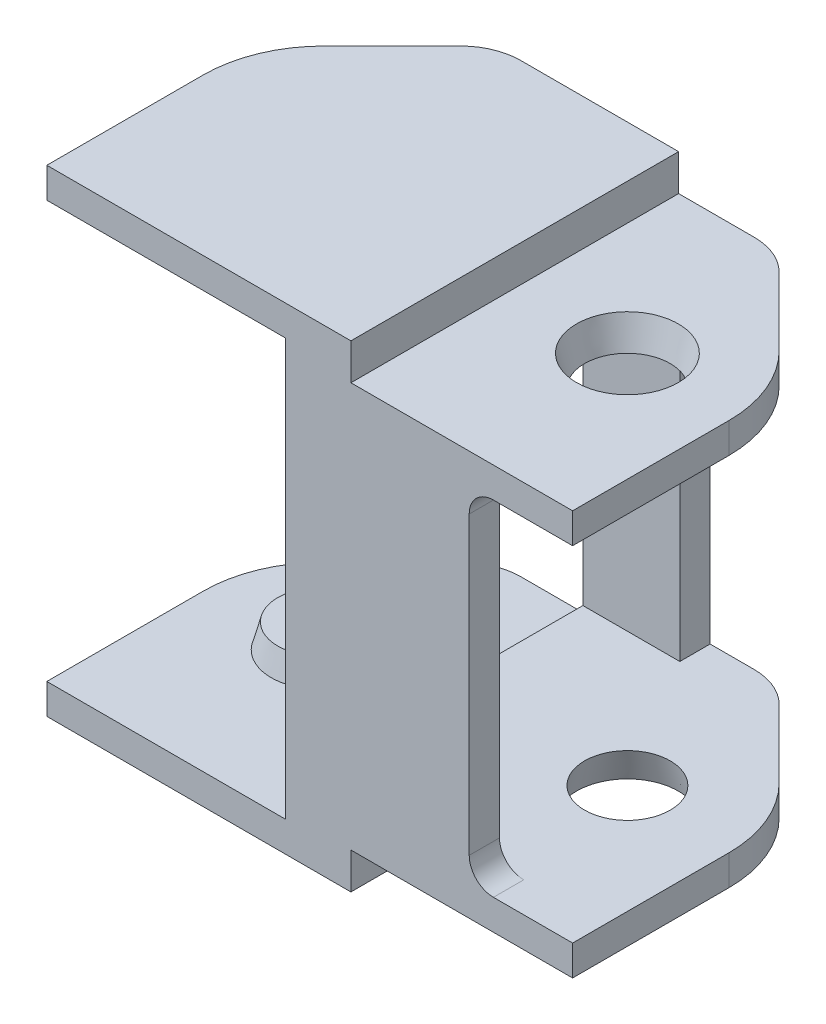
SolidWorks part; units mm, degrees
ref_plane "Front Plane" through (0, 0, 0) normal (0, 0, 1) x (1, 0, 0)
ref_plane "Top Plane" through (0, 0, 0) normal (0, 1, 0) x (1, 0, 0)
ref_plane "Right Plane" through (0, 0, 0) normal (1, 0, 0) x (0, 0, -1)
sketch "Sketch1" plane through (0, 0, 0) normal (0, 0, 1) x (1, 0, 0)
  line L0 (5.35, 1.25) -> (-4.5, 1.25)
  line L1 (9.35, 16.95) -> (9.35, 2.75)
  line L2 (-4.5, 19.7) -> (8.05, 19.7)
  line L3 (5.35, 18.45) -> (5.35, 3.25)
  line L4 (9.35, 2.75) -> (9.3789, 2.6999)
  line L5 (8.05, 1.5) -> (8.05, 0)
  line L6 (8.05, 19.7) -> (8.05, 18.2)
  line L9 (5.35, 18.45) -> (-4.5, 18.45)
  line L11 (5.35, 1.25) -> (5.35, 3.25)
  line L12 (-4.5, 0) -> (8.05, 0)
  line L13 (-4.5, 19.7) -> (-4.5, 18.45)
  line L14 (-4.5, 1.25) -> (-4.5, 0)
  line L15 (17.2, 2.75) -> (17.2, 1.5)
  line L16 (17.2, 18.2) -> (17.2, 16.95)
  line L18 (9.35, 16.95) -> (17.2, 16.95)
  line L20 (8.05, 18.2) -> (17.2, 18.2)
  line L21 (9.35, 2.75) -> (17.2, 2.75)
  line L22 (8.05, 1.5) -> (17.2, 1.5)
  point P3 (5.35, 20.7)
  point P4 (5.35, 16.7)
  point P9 (7.35, 20.7)
  point P10 (7.35, 16.7)
  dimension "D1" = 16.7
  dimension "D2" = 17.2
  dimension "D3" = 0.25
  dimension "D4" = 0.25
  dimension "D5" = 1.25
  dimension "D6" = 1.25
  dimension "D7" = 1.25
  dimension "D8" = 1.25
extrude "Boss-Extrude1" add sketch "Sketch1" along normal blind 13.525
sketch "Sketch3" plane through (9.35, 0, 0) normal (1, 0, 0) x (0, 0, -1)
  line L0 (-12.275, 16.95) -> (-1.25, 16.95)
  line L1 (-12.275, 2.75) -> (-1.25, 2.75)
  line L2 (-12.275, 16.95) -> (-12.275, 2.75)
  line L3 (-1.25, 16.95) -> (-1.25, 2.75)
  line L4 (-13.525, 2.75) -> (0, 2.75) construction
  line L5 (-13.525, 16.95) -> (0, 16.95) construction
  line L6 (0, 16.95) -> (0, 2.75) construction
  line L7 (-13.525, 16.95) -> (-13.525, 2.75) construction
  dimension "D1" = 1.25
  dimension "D2" = 1.25
extrude "Cut-Extrude1" cut sketch "Sketch3" against normal blind 5
sketch "Sketch4" plane through (0, 18.45, 0) normal (0, -1, 0) x (1, 0, 0)
  line L0 (-4.5, 6.7625) -> (0, 6.7625) construction
  line L1 (-4.5, 13.525) -> (-4.5, 0) construction
  circle A0 centre (0, 6.7625) radius 2
  dimension "D1" = 4
extrude "boss pivot" add sketch "Sketch4" along normal blind 1 draft 15
sketch "Sketch6" plane through (0, 18.2, 0) normal (0, 1, 0) x (1, 0, 0)
  line L0 (17.2, -6.7625) -> (12.7, -6.7625) construction
  line L1 (17.2, -13.525) -> (17.2, 0) construction
  circle A0 centre (12.7, -6.7625) radius 2.1
  dimension "D1" = 4.2
extrude "pivot recess" cut sketch "Sketch6" against normal up to next (1.25 mm away) draft 15
ref_plane "Plane1" through (0, 9.85, 0) normal (0, 1, 0) x (1, 0, 0)
mirror "Mirror1" about plane through (0, 9.85, 0) normal (0, 1, 0) of "pivot recess", "boss pivot"
chamfer "Chamfer5" distance 5 angle 45 4 edges at (17.2, 17.575, 0) (17.2, 2.125, 0) (-4.5, 0.625, 0) (-4.5, 19.075, 0)
fillet "Fillet2" radius 5 4 edges at (17.2, 2.125, 5) (17.2, 17.575, 5) (-4.5, 19.075, 5) (-4.5, 0.625, 5)
fillet "Fillet3" radius 2.5 4 edges at (12.2, 2.125, 0) (12.2, 17.575, 0) (0.5, 19.075, 0) (0.5, 0.625, 0)
sketch "Sketch8" plane through (0, 0, 13.525) normal (0, 0, 1) x (1, 0, 0)
  line L0 (12.9322, 16.95) -> (12.9322, 2.75)
  line L1 (12.9322, 2.75) -> (8.935, 2.75)
  line L2 (8.935, 2.75) -> (8.935, 16.95)
  line L3 (8.935, 16.95) -> (12.9322, 16.95)
extrude "Boss-Extrude4" add sketch "Sketch8" against normal up to surface (1.25 mm away) up to face at (7.35, 9.85, 12.275)
fillet "Fillet4" radius 1 2 edges at (12.9322, 16.95, 12.9) (12.9322, 2.75, 12.9)
